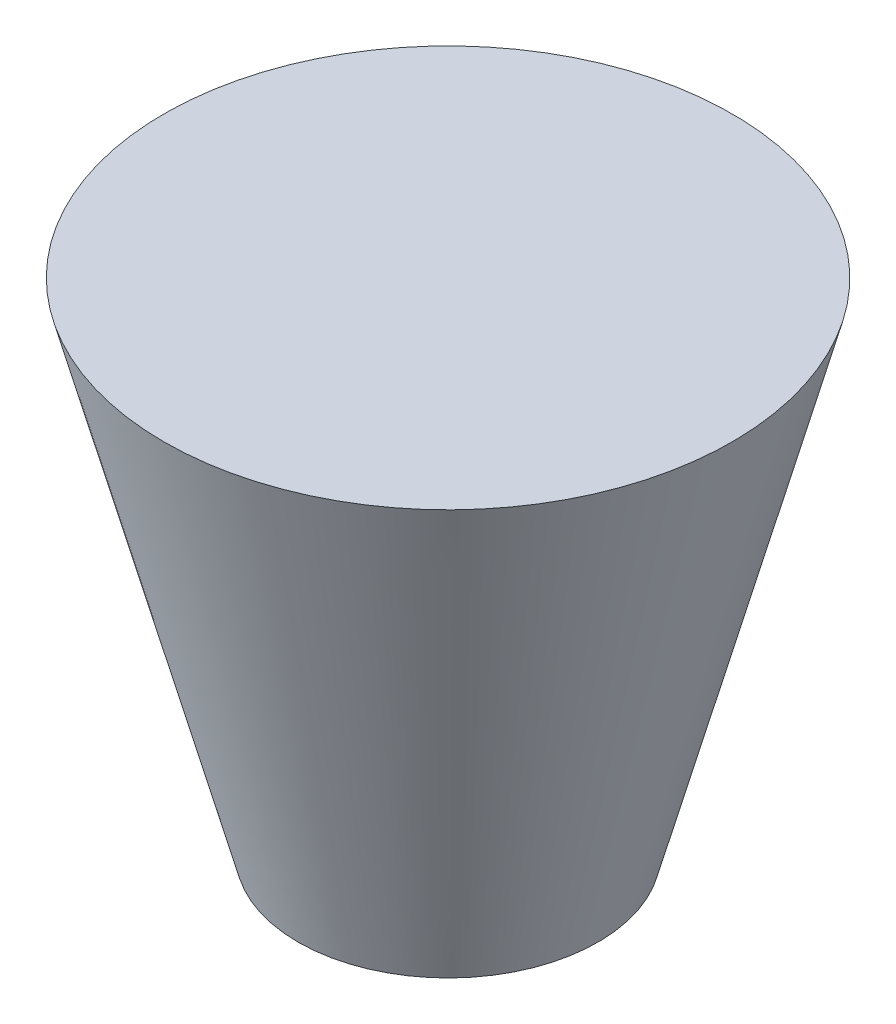
SolidWorks part; units mm, degrees
ref_plane "前视基准面" through (0, 0, 0) normal (0, 0, 1) x (1, 0, 0)
ref_plane "上视基准面" through (0, 0, 0) normal (0, 1, 0) x (1, 0, 0)
ref_plane "右视基准面" through (0, 0, 0) normal (1, 0, 0) x (0, 0, -1)
sketch "草图1" plane through (0, 0, 0) normal (0, 1, 0) x (1, 0, 0)
  circle A0 centre (-23.5032, 13.3913) radius 150
  dimension "D1" = 300
extrude "凸台-拉伸1" add sketch "草图1" along normal blind 500 draft 15 draft outward yes
